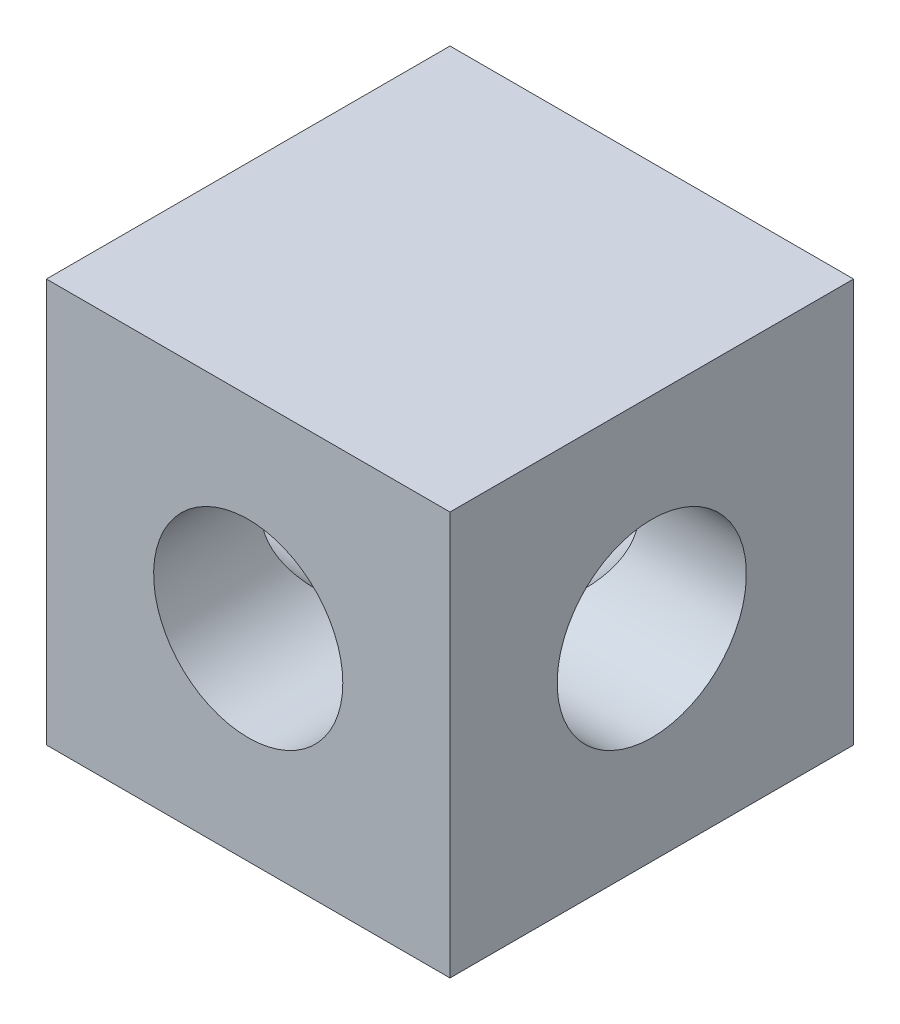
SolidWorks part; units mm, degrees
extrude "Base-Extrude" add sketch "Sketch1" along normal blind 20.32
sketch "Sketch1" plane through (0, 0, 0) normal (0, 0, 1) x (1, 0, 0)
  line L0 (-27.1383, -1.6247) -> (-6.8183, -1.6247)
  line L1 (-27.1383, -1.6247) -> (-27.1383, 18.6953)
  line L2 (-6.8183, 18.6953) -> (-27.1383, 18.6953)
  line L3 (-6.8183, 18.6953) -> (-6.8183, -1.6247)
  line L4 (-6.8183, 18.6953) -> (-27.1383, -1.6247) construction
  circle A0 centre (-16.9783, 8.5353) radius 4.7625
  dimension "hole_dependent" = 9.525
  dimension "D1" = 20.32
  dimension "D2" = 20.32
material "AISI 321 Annealed Stainless Steel (SS)"
ref_plane "Front" through (0, 0, 0) normal (0, 0, 1) x (1, 0, 0)
ref_plane "Top" through (0, 0, 0) normal (0, 1, 0) x (-1, 0, 0)
ref_plane "Right" through (0, 0, 0) normal (1, 0, 0) x (0, 0, -1)
sketch "Sketch3" plane through (-6.8183, 0, 0) normal (1, 0, 0) x (0, 0, -1)
  line L0 (0, 18.6953) -> (-20.32, -1.6247) construction
  circle A0 centre (-10.16, 8.5353) radius 4.7625
extrude "Cut-Extrude1" cut sketch "Sketch3" against normal through all
equation "\"hole_dependent@Sketch1\" = \"hole-independent@Sketch3\""
